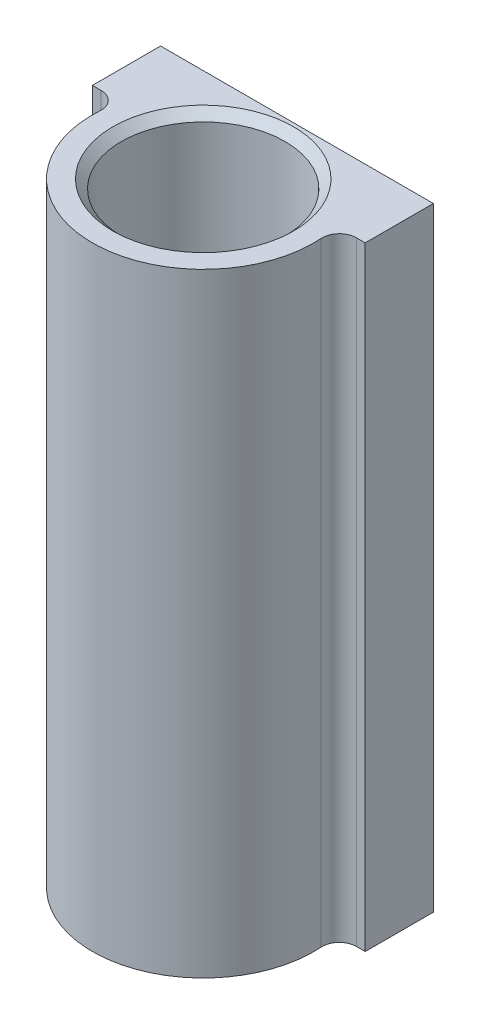
SolidWorks part; units mm, degrees
ref_plane "Front Plane" through (0, 0, 0) normal (0, 0, 1) x (1, 0, 0)
ref_plane "Top Plane" through (0, 0, 0) normal (0, 1, 0) x (1, 0, 0)
ref_plane "Right Plane" through (0, 0, 0) normal (1, 0, 0) x (0, 0, -1)
sketch "Sketch1" plane through (0, 0, 0) normal (0, 1, 0) x (1, 0, 0)
  line L0 (14.9666, 3) -> (16, 3)
  line L1 (-16, 11) -> (16, 11)
  line L2 (-16, 11) -> (-16, 3)
  line L3 (-16, 3) -> (-14.9666, 3)
  line L4 (16, 11) -> (16, 3)
  circle A0 centre (0, 0) radius 9.6
  arc A1 (-12.9711, 0.8667) -> (12.9711, 0.8667) centre (0, 0) ccw
  arc A3 (-12.9711, 0.8667) -> (-14.9666, 3) centre (-14.9666, 1) ccw
  arc A4 (14.9666, 3) -> (12.9711, 0.8667) centre (14.9666, 1) ccw
  dimension "D1" = 19.2
  dimension "D2" = 13
  dimension "D6" = 2
  dimension "D11" = 2
  dimension "D3" = 32
  dimension "D4" = 8
  dimension "D5" = 11
  dimension "D9" = 16
extrude "Boss-Extrude1" add sketch "Sketch1" along normal blind 72
sketch "Sketch2" plane through (0, 0, -11) normal (0, 0, 1) x (1, 0, 0)
  line L0 (-11, 67) -> (11, 5) construction
  line L1 (0, 36) -> (0, 0) construction
  line L2 (-16, 36) -> (0, 36) construction
  line L3 (-16, 72) -> (-16, 0) construction
  circle A0 centre (-11, 67) radius 2.6
  circle A1 centre (-11, 5) radius 2.6
  circle A2 centre (11, 67) radius 2.6
  circle A3 centre (11, 5) radius 2.6
  point P12 (0, 0)
  dimension "D1" = 5.2
  dimension "D2" = 5
  dimension "D3" = 62
extrude "Cut-Extrude1" cut sketch "Sketch2" along normal blind 6
chamfer "Chamfer1" distance 0.5 angle 45 4 edges at (-8.4, 5, -11) (13.6, 5, -11) (13.6, 67, -11) (-8.4, 67, -11)
chamfer "Chamfer2" distance 1 angle 45 2 edges at (0, 0, 9.6) (0, 72, 9.6)
